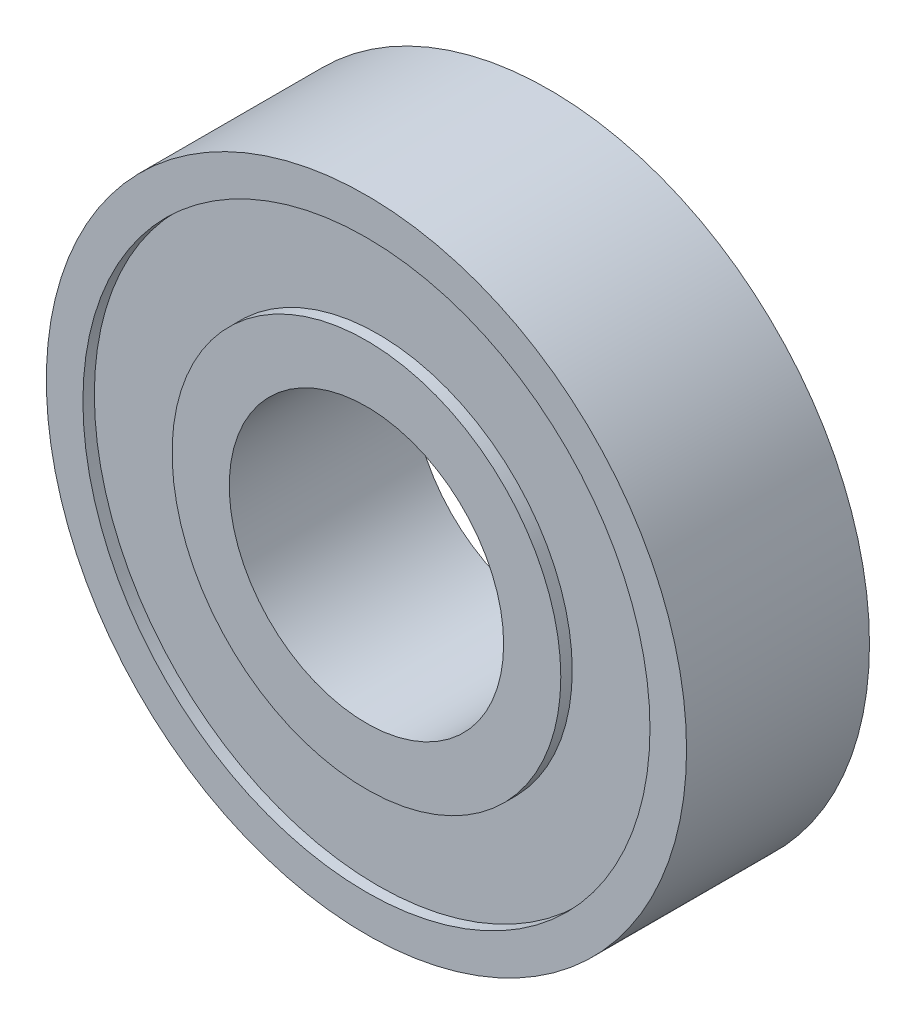
SolidWorks part; units mm, degrees
material "201 退火不鏽鋼 (SS)"
ref_plane "前基準面" through (0, 0, 0) normal (0, 0, 1) x (1, 0, 0)
ref_plane "上基準面" through (0, 0, 0) normal (0, 1, 0) x (1, 0, 0)
ref_plane "右基準面" through (0, 0, 0) normal (1, 0, 0) x (0, 0, -1)
sketch "草圖1" plane through (0, 0, 0) normal (0, 0, 1) x (1, 0, 0)
  circle A0 centre (0, 0) radius 14
  dimension "D1" = 28
extrude "填料-伸長1" add sketch "草圖1" along normal mid plane 8
sketch "草圖2" plane through (0, 0, 4) normal (0, 0, 1) x (1, 0, 0)
  circle A0 centre (0, 0) radius 6
  dimension "D1" = 12
extrude "除料-伸長1" cut sketch "草圖2" against normal through all
sketch "草圖3" plane through (0, 0, 4) normal (0, 0, 1) x (1, 0, 0)
  circle A0 centre (0, 0) radius 8.5
  circle A1 centre (0, 0) radius 12.4
  dimension "D1" = 24.8
  dimension "D2" = 17
extrude "除料-伸長2" cut sketch "草圖3" against normal blind 0.5
mirror "鏡射1" about plane through (0, 0, 0) normal (0, 0, 1) of "除料-伸長2"
